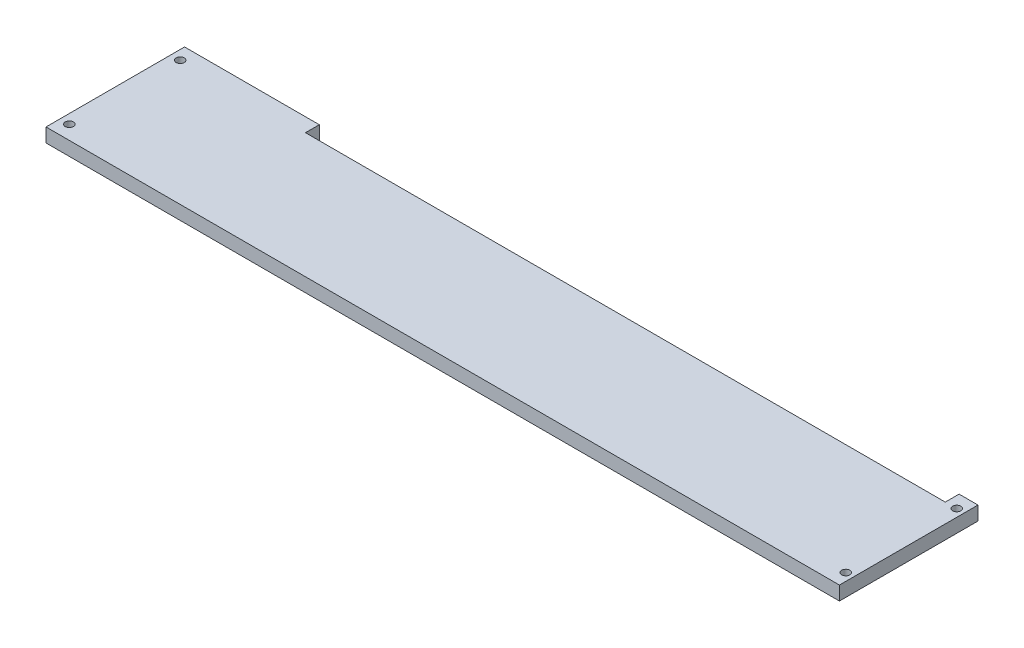
SolidWorks part; units mm, degrees
material "1060 Alloy"
ref_plane "Front Plane" through (0, 0, 0) normal (0, 0, 1) x (1, 0, 0)
ref_plane "Top Plane" through (0, 0, 0) normal (0, 1, 0) x (1, 0, 0)
ref_plane "Right Plane" through (0, 0, 0) normal (1, 0, 0) x (0, 0, -1)
sketch "Sketch1" plane through (0, 0, 0) normal (0, 1, 0) x (1, 0, 0)
  line L0 (532.64, 0) -> (545.64, 0)
  line L1 (0, 0) -> (92.64, 0)
  line L2 (0, 0) -> (0, -95.3)
  line L3 (0, -95.3) -> (545.64, -95.3)
  line L4 (545.64, 0) -> (545.64, -95.3)
  line L5 (92.64, 0) -> (532.64, 0) construction
  line L6 (92.64, 0) -> (92.64, -9.5)
  line L7 (92.64, -9.5) -> (532.64, -9.5)
  line L8 (532.64, 0) -> (532.64, -9.5)
  dimension "D1" = 545.64
  dimension "D2" = 95.3
  dimension "D3" = 13
  dimension "D4" = 440
  dimension "D5" = 9.5
extrude "Boss-Extrude1" add sketch "Sketch1" along normal blind 9.55
sketch "Sketch2" plane through (0, 9.55, 0) normal (0, 1, 0) x (-1, 0, 0)
  line L0 (-92.64, 0) -> (0, 0) construction
  line L1 (0, 0) -> (0, 95.3) construction
  line L2 (-540.4, 9.38) -> (-540.4, 85.68) construction
  line L3 (-6.4, 9.38) -> (-6.4, 85.68) construction
  line L6 (0, 95.3) -> (-545.64, 95.3) construction
  line L8 (0, 0) -> (0, 95.3) construction
  line L9 (-6.4, 90.29) -> (-6.4, 95.3) construction
  line L10 (-1.79, 85.68) -> (0, 85.68) construction
  line L11 (-540.4, 85.68) -> (-6.4, 85.68) construction
  line L12 (-540.4, 9.38) -> (-6.4, 9.38) construction
  line L13 (-545.01, 85.68) -> (-545.64, 85.68) construction
  line L14 (-545.64, 95.3) -> (-545.64, 0) construction
  circle A0 centre (-6.4, 9.38) radius 4.61 construction
  circle A1 centre (-6.4, 85.68) radius 4.61 construction
  circle A8 centre (-540.4, 9.38) radius 4.61 construction
  circle A9 centre (-540.4, 85.68) radius 4.61 construction
  circle A10 centre (-6.4, 9.38) radius 2.795
  circle A11 centre (-6.4, 85.68) radius 2.795
  circle A14 centre (-540.4, 85.68) radius 2.795
  circle A15 centre (-540.4, 9.38) radius 2.795
  dimension "D1" = 5.59
  dimension "D2" = 9.22
  dimension "D3" = 9.38
  dimension "D4" = 6.4
  dimension "D5" = 76.3
  dimension "D6" = 534
extrude "Cut-Extrude1" cut sketch "Sketch2" against normal up to next
sketch "Sketch5" plane through (0, 0, 0) normal (0, -1, 0) x (1, 0, 0)
  circle A0 centre (6.4, 85.68) radius 4.61
  circle A1 centre (6.4, 9.38) radius 4.61
  circle A2 centre (540.4, 9.38) radius 4.61
  circle A3 centre (540.4, 85.68) radius 4.61
  circle A4 centre (6.4, 9.38) radius 2.795 construction
  dimension "D1" = 9.22
  dimension "D2" = 9.22
  dimension "D3" = 9.22
  dimension "D4" = 9.22
extrude "Cut-Extrude3" cut sketch "Sketch5" against normal blind 5.2
